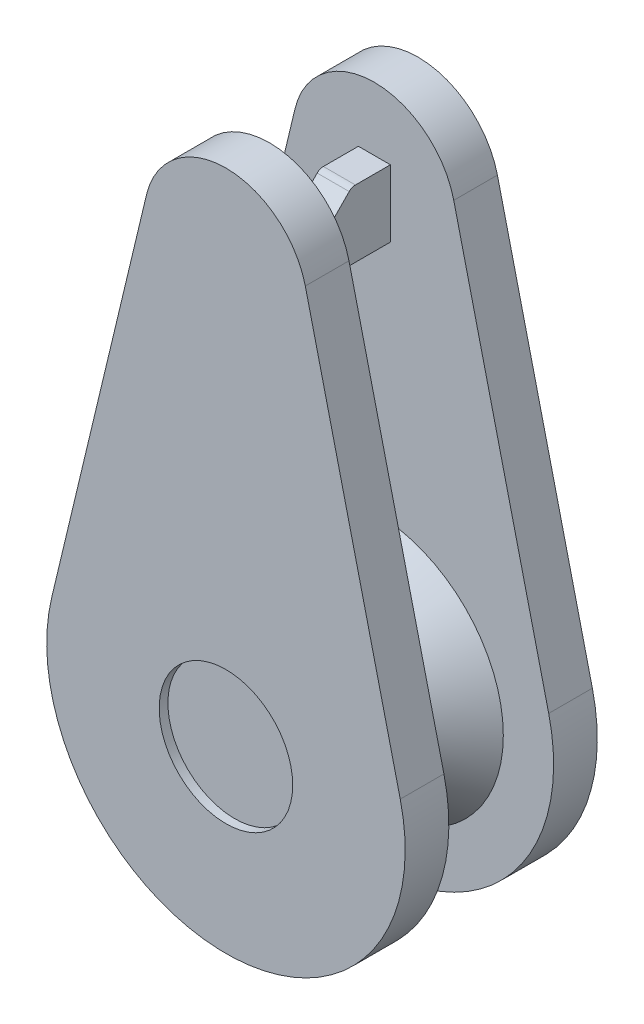
SolidWorks part; units mm, degrees
ref_plane "前视基准面" through (0, 0, 0) normal (0, 0, 1) x (1, 0, 0)
ref_plane "上视基准面" through (0, 0, 0) normal (0, 1, 0) x (1, 0, 0)
ref_plane "右视基准面" through (0, 0, 0) normal (1, 0, 0) x (0, 0, -1)
sketch "草图2" plane through (0, 0, 0) normal (0, 0, 1) x (1, 0, 0)
  line L0 (20.5077, 136.955) -> (22.6814, 146.0419)
  line L1 (26.3178, 146.0451) -> (28.4923, 136.955)
  arc A0 (20.5077, 136.955) -> (28.4923, 136.955) centre (24.5, 136) ccw
  arc A1 (22.6814, 146.0419) -> (26.3178, 146.0451) centre (24.5, 145.6069) cw
extrude "凸台-拉伸1" add sketch "草图2" along normal blind 1
sketch "草图3" plane through (0, 0, 1) normal (0, 0, 1) x (1, 0, 0)
  circle A0 centre (24.5, 136) radius 2.9527
ref_plane "基准面1" through (0, 0, 2.2) normal (0, 0, -1) x (-1, 0, 0)
sketch "草图5" plane through (0, 0, 2.2) normal (0, 0, -1) x (-1, 0, 0)
  circle A0 centre (-24.5, 136) radius 1.7382
loft "放样2" add profiles "草图3", "草图5"
sketch "草图6" plane through (0, 0, 1) normal (0, 0, 1) x (1, 0, 0)
  line L1 (24.1334, 146.0244) -> (24.8666, 146.0244)
  line L2 (24.1334, 146.0244) -> (24.1334, 144.4907)
  line L3 (24.1334, 144.4907) -> (24.8666, 144.4907)
  line L4 (24.8666, 146.0244) -> (24.8666, 144.4907)
  line L5 (24.1334, 146.0244) -> (24.8666, 144.4907) construction
  line L6 (24.1334, 144.4907) -> (24.8666, 146.0244) construction
  point P0 (24.5, 145.2576)
extrude "凸台-拉伸2" add sketch "草图6" along normal blind 2.4
sketch "草图7" plane through (24.1334, 0, 0) normal (-1, 0, 0) x (0, 0, 1)
  line L0 (1.8847, 146.0244) -> (3.4, 144.4907)
  line L1 (3.4, 146.0244) -> (1, 146.0244) construction
  line L2 (3.4, 144.4907) -> (3.4, 146.0244)
  line L3 (3.4, 146.0244) -> (1.8847, 146.0244)
extrude "切除-拉伸1" cut sketch "草图7" against normal blind 2.4
fillet "圆角1" radius 0.2 2 edges at (24.5, 144.4907, 3.4) (24.5, 146.0244, 1.8847)
mirror "镜向4" about plane through (0, 0, 2.2) normal (0, 0, -1) of "放样2", "凸台-拉伸1"
mirror "镜向5" about plane through (0, 0, 2.2) normal (0, 0, -1) of "凸台-拉伸1"
fillet "圆角2" radius 0.2 1 edges at (22.7618, 136, 2.2)
sketch "草图8" plane through (0, 0, 4.4) normal (0, 0, 1) x (1, 0, 0)
  circle A0 centre (24.5, 136) radius 1.5294
extrude "切除-拉伸3" cut sketch "草图8" against normal blind 0.2
